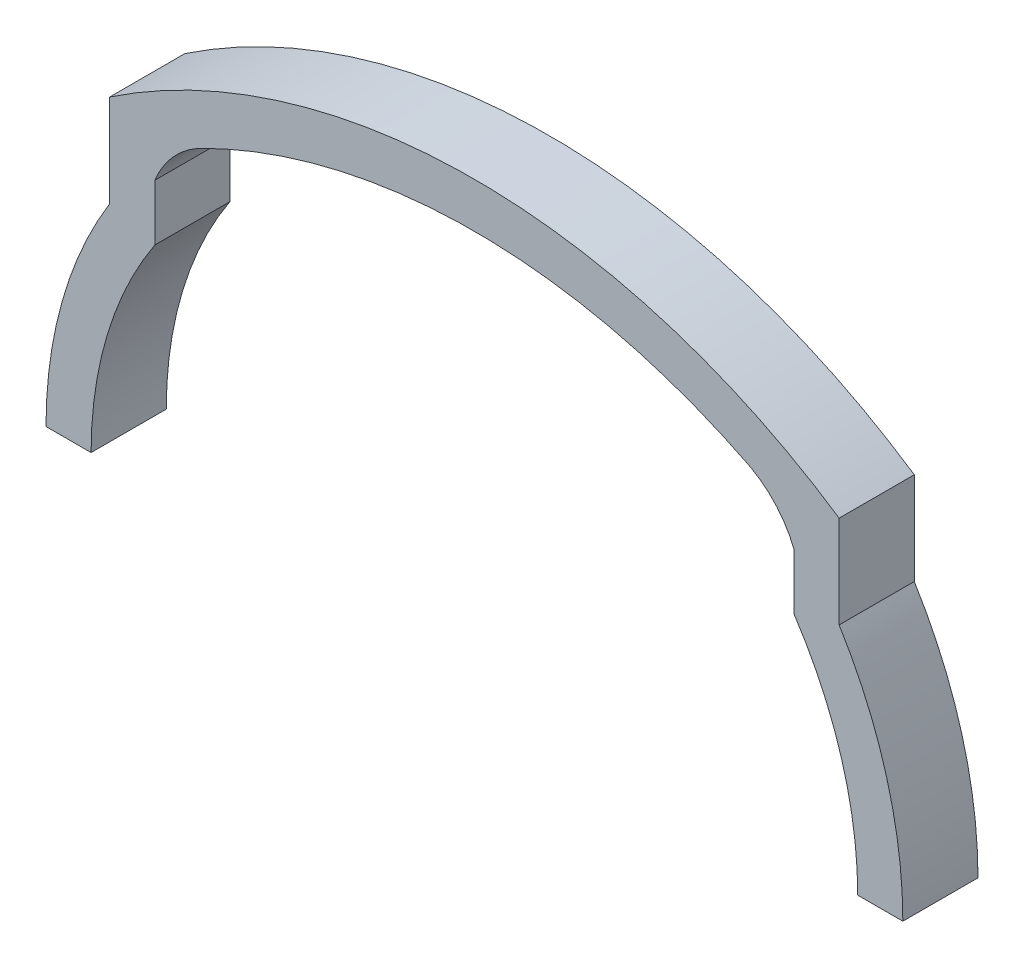
SolidWorks part; units mm, degrees
ref_plane "Front Plane" through (0, 0, 0) normal (0, 0, 1) x (1, 0, 0)
ref_plane "Top Plane" through (0, 0, 0) normal (0, 1, 0) x (1, 0, 0)
ref_plane "Right Plane" through (0, 0, 0) normal (1, 0, 0) x (0, 0, -1)
sketch "Sketch1" plane through (0, 0, 0) normal (0, 0, 1) x (1, 0, 0)
  line L1 (67.3394, 0) -> (0, 0) construction
  line L2 (0, 0) -> (0, 65.2519) construction
  line L4 (-21, 19.0441) -> (-19.1593, 16.06) construction
  line L5 (21, 19.0441) -> (19.1593, 16.06) construction
  line L6 (-25.5, 0) -> (25.5, 0)
  line L8 (-21.2625, 17.8066) -> (-21.2625, 14.0768)
  line L9 (21.2625, 17.8066) -> (21.2625, 14.0768)
  line L12 (24.2625, 21.1051) -> (24.2625, 14.9526)
  line L13 (-24.2625, 21.1051) -> (-24.2625, 14.9526)
  line L14 (-28.5, 0) -> (28.5, 0)
  line L15 (-21.2625, 19.4696) -> (-21.2625, 14.0768) construction
  line L16 (21.2625, 19.4696) -> (21.2625, 14.0768) construction
  line L17 (-28.3417, -3) -> (28.3417, -3) construction
  arc A2 (21, 19.0441) -> (-21, 19.0441) centre (0, -15) ccw construction
  arc A4 (25.5, 0) -> (21.2625, 14.0768) centre (0, 0) ccw
  arc A6 (18.3615, 21.0986) -> (-18.3615, 21.0986) centre (0, -15) ccw
  arc A8 (-21.2625, 14.0768) -> (-25.5, 0) centre (0, 0) ccw
  arc A9 (25.5, 0) -> (-25.5, 0) centre (0, 0) ccw construction
  arc A10 (25, 0) -> (-25, 0) centre (0, 0) ccw construction
  arc A11 (28.5, 0) -> (24.2625, 14.9526) centre (0, 0) ccw
  arc A12 (24.2625, 21.1051) -> (-24.2625, 21.1051) centre (0, -15) ccw
  arc A13 (-24.2625, 14.9526) -> (-28.5, 0) centre (0, 0) ccw
  arc A14 (-24.2625, 14.9526) -> (-28.3417, -3) centre (0, 0) ccw construction
  arc A15 (28.3417, -3) -> (24.2625, 14.9526) centre (0, 0) ccw construction
  arc A16 (-21.2625, 17.8066) -> (-18.3615, 21.0986) centre (-15.2227, 15.4083) cw
  arc A17 (21.2625, 17.8066) -> (18.3615, 21.0986) centre (15.2227, 15.4083) ccw
  arc A18 (21.2625, 19.4696) -> (-21.2625, 19.4696) centre (0, -15) ccw construction
  point P4 (0, 25)
  point P5 (0, 25)
  point P34 (-17.6696, 21.4422)
  point P36 (-21.2625, 17.2012)
  point P37 (-18.3615, 21.1051)
  point P38 (-21.2625, 17.8066)
  dimension "D1" = 25
  dimension "D2" = 80
  dimension "D3" = 42
  dimension "D4" = 0.5
  dimension "D5" = 3
extrude "Boss-Extrude2" add sketch "Sketch1" along normal blind 5 contours A17 L9 A4 L14 A11 L12 A12 L13 A13 A8 L8 A16 A6
